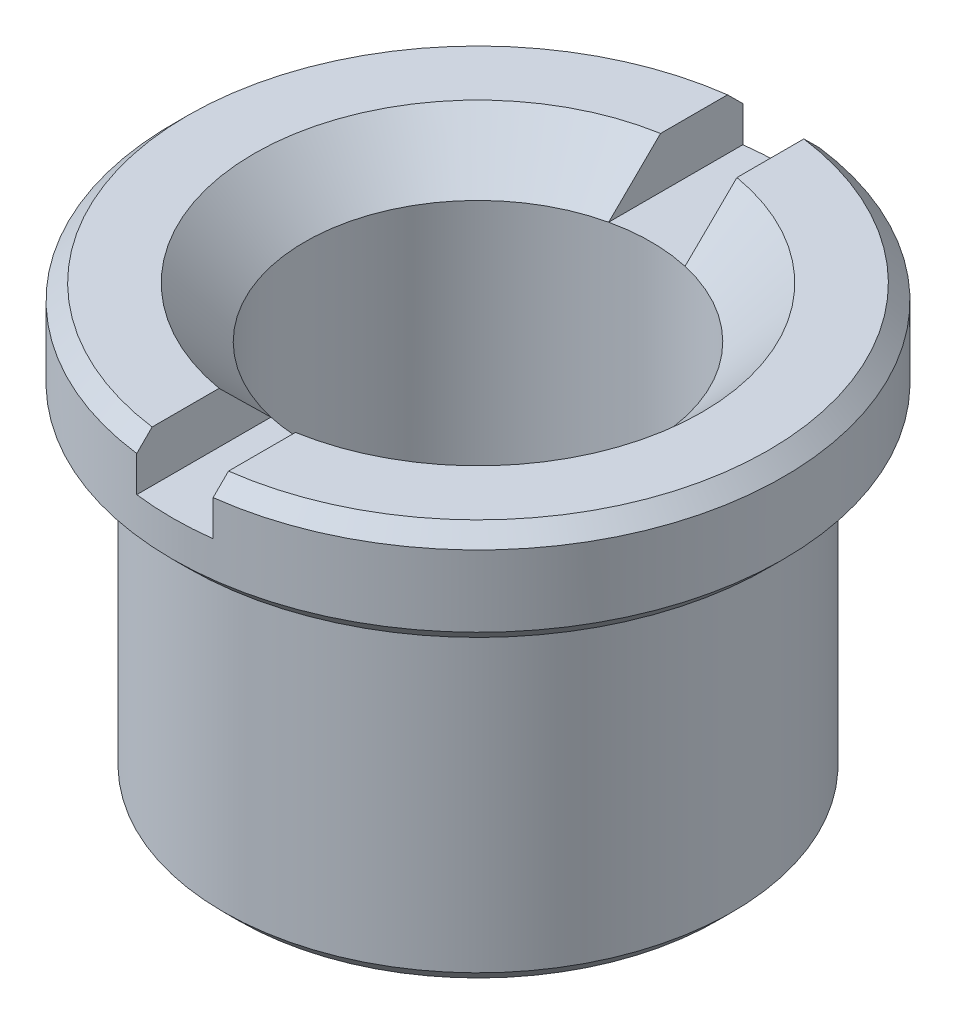
SolidWorks part; units mm, degrees
ref_plane "Plan de face" through (0, 0, 0) normal (0, 0, 1) x (1, 0, 0)
ref_plane "Plan de dessus" through (0, 0, 0) normal (0, 1, 0) x (1, 0, 0)
ref_plane "Plan de droite" through (0, 0, 0) normal (1, 0, 0) x (0, 0, -1)
sketch "Esquisse1" plane through (0, 0, 0) normal (0, 1, 0) x (1, 0, 0)
  circle A0 centre (0, 0) radius 5
  dimension "D1" = 10
extrude "Extrusion1" add sketch "Esquisse1" against normal blind 6.5
sketch "Esquisse2" plane through (0, 0, 0) normal (0, 1, 0) x (-1, 0, 0)
  circle A0 centre (0, 0) radius 6
  dimension "D1" = 12
extrude "Extrusion2" add sketch "Esquisse2" along normal blind 2
sketch "Esquisse3" plane through (0, 2, 0) normal (0, 1, 0) x (-1, 0, 0)
  circle A0 centre (0, 0) radius 3.4
  dimension "D1" = 6.8
extrude "Enlèv. mat.-Extru.1" cut sketch "Esquisse3" against normal through all
chamfer "Chanfrein1" distance 0.3 angle 45 3 edges at (0, -6.5, 5) (0, 0, 6) (0, 2, 6)
chamfer "Chanfrein2" distance 1 angle 45 1 edges at (0, 2, 3.4)
sketch "Esquisse4" plane through (0, 2, 0) normal (0, 1, 0) x (-1, 0, 0)
  line L0 (0, -6.408) -> (0, 6.4785) construction
  line L2 (0.75, -6) -> (-0.75, -6)
  line L3 (0.75, -6) -> (0.75, 6)
  line L4 (0.75, 6) -> (-0.75, 6)
  line L5 (-0.75, -6) -> (-0.75, 6)
  circle A0 centre (0, 0) radius 6 construction
  dimension "D1" = 1.5
extrude "Enlèv. mat.-Extru.2" cut sketch "Esquisse4" against normal blind 1
